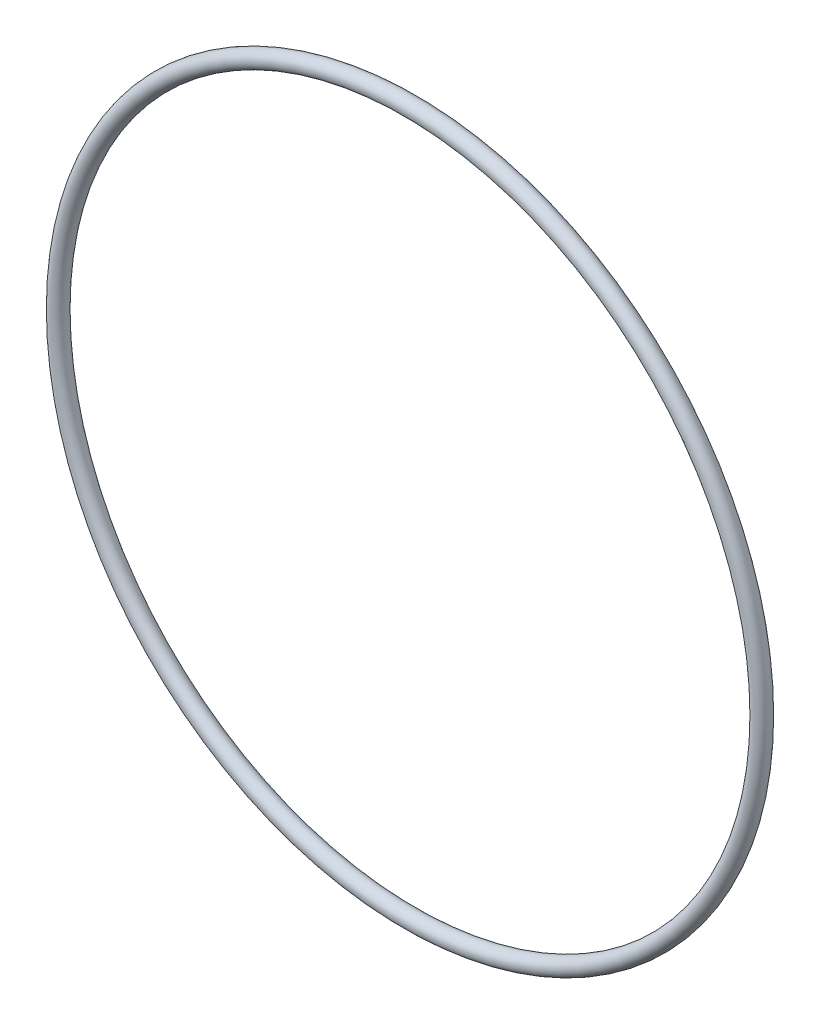
SolidWorks part; units mm, degrees
ref_plane "Front" through (0, 0, 0) normal (0, 0, 1) x (1, 0, 0)
ref_plane "Top" through (0, 0, 0) normal (0, 1, 0) x (1, 0, 0)
ref_plane "Right" through (0, 0, 0) normal (1, 0, 0) x (0, 0, -1)
sketch "Sketch1" plane through (0, 0, 0) normal (1, 0, 0) x (0, -1, 0)
  line L0 (0, -0.889) -> (0, 0.889) construction
  line L2 (-41.9659, 0) -> (41.9659, 0) construction
  line L3 (-36.3728, 0) -> (36.3728, 0) construction
  circle A0 centre (37.2618, 0) radius 0.889
  point P9 (36.3728, 0)
  point P10 (38.1508, 0)
  point P13 (37.2618, 0.889)
  point P14 (37.2618, -0.889)
  dimension "Width" = 1.778
  dimension "ID" = 72.7456
revolve "Revolve1" add sketch "Sketch1" angle 360 about L0
